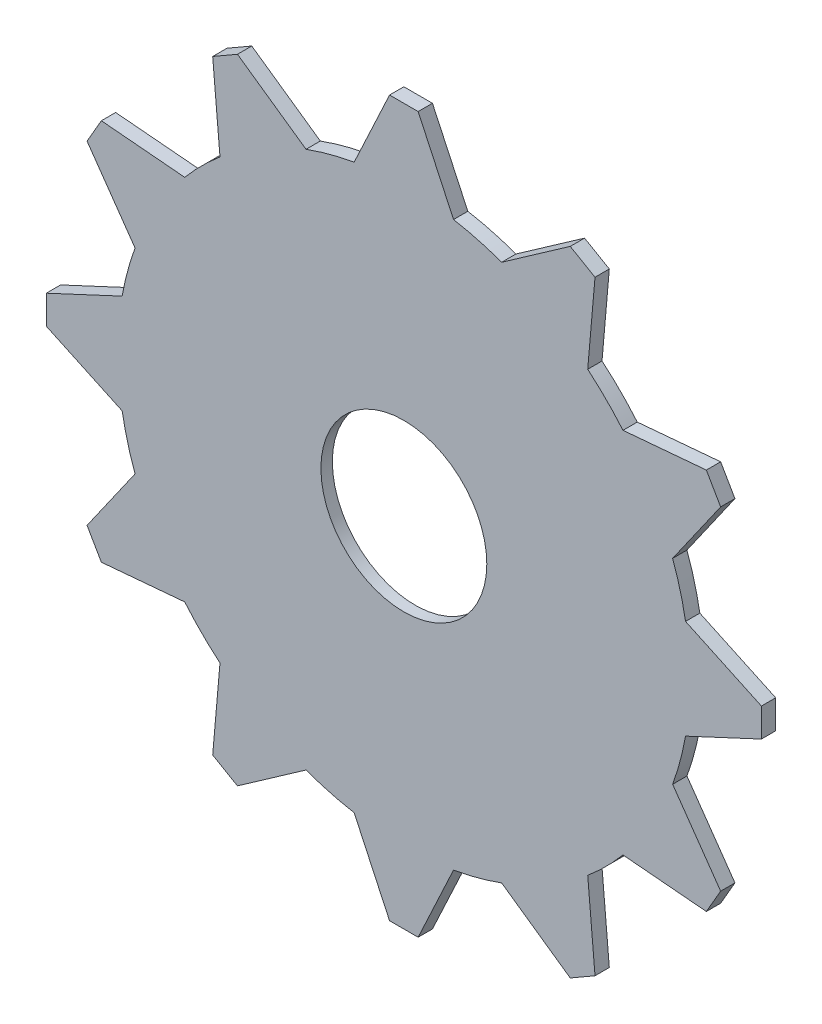
SolidWorks part; units mm, degrees
ref_plane "Front Plane" through (0, 0, 0) normal (0, 0, 1) x (1, 0, 0)
ref_plane "Top Plane" through (0, 0, 0) normal (0, 1, 0) x (1, 0, 0)
ref_plane "Right Plane" through (0, 0, 0) normal (1, 0, 0) x (0, 0, -1)
sketch "Sketch1" plane through (0, 0, 0) normal (0, 0, 1) x (1, 0, 0)
  circle A0 centre (0, 0) radius 25.4
  dimension "D1" = 50.8
extrude "Boss-Extrude1" add sketch "Sketch1" along normal blind 1.27
sketch "Sketch2" plane through (0, 0, 1.27) normal (0, 0, 1) x (1, 0, 0)
  line L0 (0, 25.4) -> (0, 31.75) construction
  line L1 (-1.27, 31.75) -> (1.27, 31.75)
  line L2 (1.27, 31.75) -> (4.411, 25.0141)
  line L3 (-1.27, 31.75) -> (-4.411, 25.0141)
  line L4 (70, -22.38) -> (63.2641, -19.239)
  line L5 (70, -22.38) -> (70, -24.92)
  line L6 (70, -24.92) -> (63.2641, -28.061)
  line L7 (15.87, -93.65) -> (19.011, -86.9141)
  line L8 (15.87, -93.65) -> (13.33, -93.65)
  line L9 (13.33, -93.65) -> (10.189, -86.9141)
  line L10 (-55.4, -39.52) -> (-48.6641, -42.661)
  line L11 (-55.4, -39.52) -> (-55.4, -36.98)
  line L12 (-55.4, -36.98) -> (-48.6641, -33.839)
  circle A0 centre (0, 0) radius 25.4 construction
  arc A1 (4.411, 25.0141) -> (-4.411, 25.0141) centre (0, 0) ccw
  point P25 (7.3, -30.95)
  circle M1 centre (0, 0) radius 25.4
  dimension "D1" = 1.27
  dimension "D2" = 4
  dimension "D3" = 6.35
  dimension "D4" = 65
extrude "Boss-Extrude2" add sketch "Sketch2" against normal blind 1.27 contours L12 L11 L10 M1 | A1 L0 L1 L3 | L0 L2 L1 M1 | L6 L5 L4 M1 | L9 L8 L7 M1
sketch "Sketch3" plane through (0, 0, 0) normal (0, 0, -1) x (-1, 0, 0)
  circle A0 centre (0, 0) radius 7.366
  dimension "D1" = 14.732
extrude "Cut-Extrude1" cut sketch "Sketch3" against normal blind 10
pattern_circular "CirPattern1" count 12 every 30 about axis through (0, 0, 0) along (0, 0, 1) of "Boss-Extrude2"
sketch "Sketch4" plane through (0, 0, 0) normal (0, 0, -1) x (-1, 0, 0)
  circle A0 centre (0, 0) radius 18.2832
extrude "Cut-Extrude2" cut sketch "Sketch4" against normal blind 0.254
